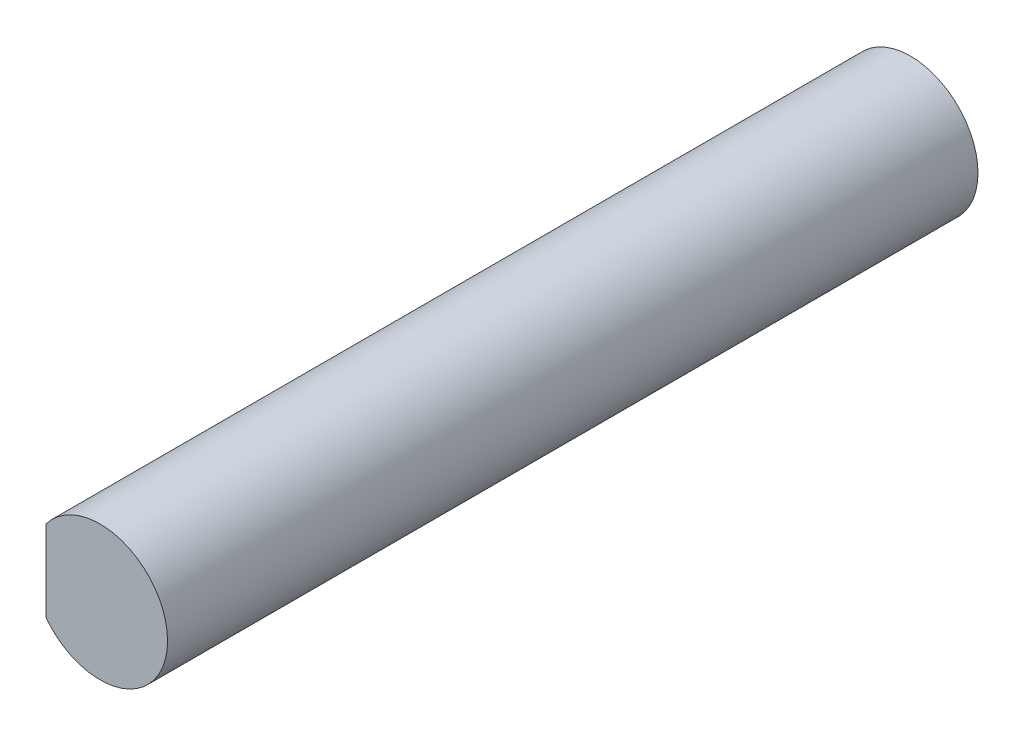
SolidWorks part; units mm, degrees
ref_plane "Front Plane" through (0, 0, 0) normal (0, 0, 1) x (1, 0, 0)
ref_plane "Top Plane" through (0, 0, 0) normal (0, 1, 0) x (1, 0, 0)
ref_plane "Right Plane" through (0, 0, 0) normal (1, 0, 0) x (0, 0, -1)
sketch "Sketch1" plane through (0, 0, 0) normal (0, 0, 1) x (1, 0, 0)
  circle A0 centre (0, 0) radius 5
  dimension "D1" = 10
extrude "Boss-Extrude1" add sketch "Sketch1" along normal blind 60 from offset 10
sketch "Sketch2" plane through (0, 0, 70) normal (0, 0, 1) x (1, 0, 0)
  line L0 (-4, 3) -> (-4, -3)
  circle A0 centre (0, 0) radius 5 construction
  arc A1 (-4, 3) -> (-4, -3) centre (0, 0) ccw
  dimension "D1" = 4
extrude "Cut-Extrude1" cut sketch "Sketch2" against normal blind 7
